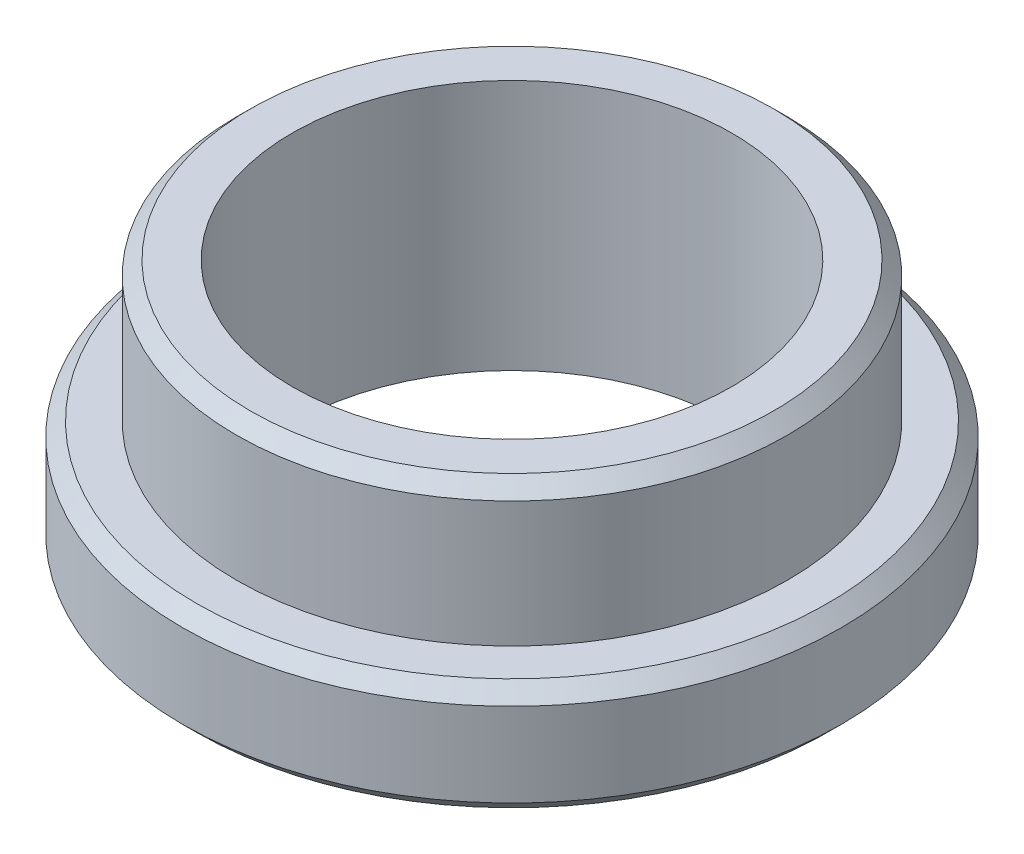
SolidWorks part; units mm, degrees
ref_plane "Front Plane" through (0, 0, 0) normal (0, 0, 1) x (1, 0, 0)
ref_plane "Top Plane" through (0, 0, 0) normal (0, 1, 0) x (1, 0, 0)
ref_plane "Right Plane" through (0, 0, 0) normal (1, 0, 0) x (0, 0, -1)
sketch "Sketch1" plane through (0, 0, 0) normal (0, 0, 1) x (1, 0, 0)
  line L0 (0, 0) -> (0, -16.7273) construction
  line L1 (5.016, 0) -> (5.016, -2.54)
  line L2 (5.016, -2.54) -> (6, -2.54)
  line L3 (6, -2.54) -> (6, -4.572)
  line L4 (6, -4.572) -> (4, -4.572)
  line L6 (4, 0) -> (5.016, 0)
  line L8 (4, -4.572) -> (4, 0)
  dimension "D1" = 1.016
  dimension "D2" = 2.54
  dimension "D3" = 2.032
  dimension "D4" = 8
  dimension "D5" = 12
revolve "Revolve1" add sketch "Sketch1" angle 360 about L0
chamfer "Chamfer1" distance 0.254 angle 45 3 edges at (0, -4.572, 6) (0, -2.54, 6) (0, 0, 5.016)
